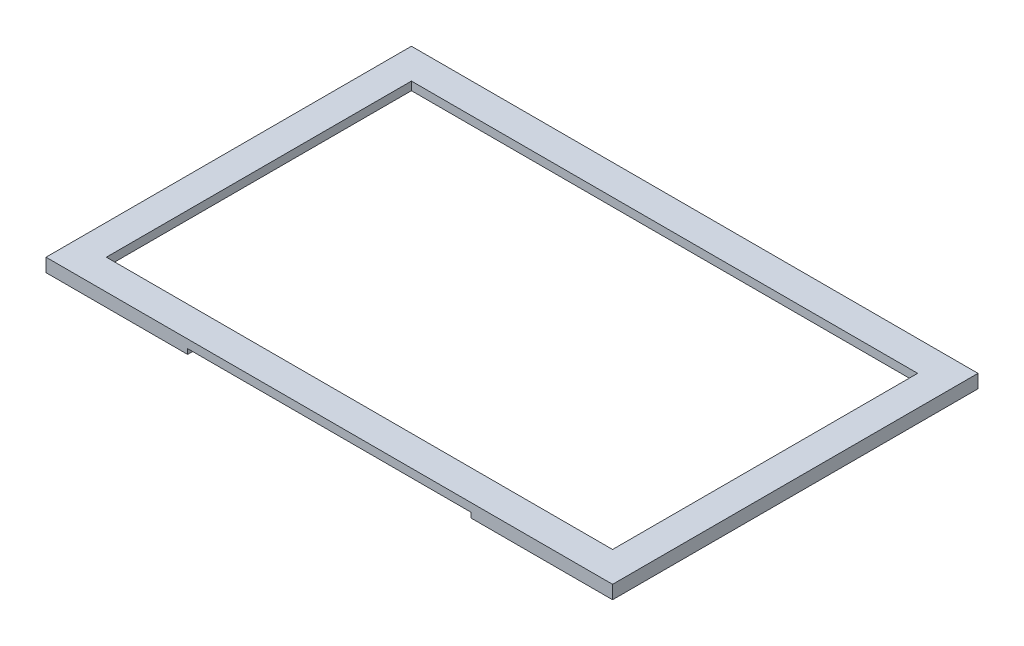
SolidWorks part; units mm, degrees
ref_plane "Front Plane" through (0, 0, 0) normal (0, 0, 1) x (1, 0, 0)
ref_plane "Top Plane" through (0, 0, 0) normal (0, 1, 0) x (1, 0, 0)
ref_plane "Right Plane" through (0, 0, 0) normal (1, 0, 0) x (0, 0, -1)
sketch "Sketch1" plane through (0, 0, 0) normal (0, 0, 1) x (1, 0, 0)
  line L1 (0, 0) -> (169, 0)
  line L2 (0, 0) -> (0, 4)
  line L3 (0, 4) -> (169, 4)
  line L4 (169, 0) -> (169, 4)
  dimension "D1" = 169
  dimension "D2" = 4
extrude "Boss-Extrude1" add sketch "Sketch1" against normal blind 109
sketch "Sketch3" plane through (0, 0, 0) normal (0, -1, 0) x (1, 0, 0)
  line L2 (169, -109) -> (169, 0) construction
  line L3 (167, -107) -> (2, -107)
  line L4 (167, -107) -> (167, -2)
  line L5 (167, -2) -> (2, -2)
  line L6 (2, -107) -> (2, -2)
  line L7 (167, -107) -> (2, -2) construction
  line L8 (167, -2) -> (2, -107) construction
  line L9 (169, -109) -> (0, -109) construction
  point P0 (84.5, -54.5)
  point P5 (84.5, -54.5)
  dimension "D1" = 84.5
  dimension "D2" = 54.5
  dimension "D3" = 105
  dimension "D4" = 165
extrude "Cut-Extrude1" cut sketch "Sketch3" against normal blind 1.5
sketch "Sketch4" plane through (0, 4, 0) normal (0, 1, 0) x (1, 0, 0)
  line L0 (169, 109) -> (169, 0) construction
  line L1 (169, 0) -> (0, 0) construction
  line L3 (160, 9) -> (9, 9)
  line L4 (160, 9) -> (160, 100)
  line L5 (160, 100) -> (9, 100)
  line L6 (9, 9) -> (9, 100)
  line L7 (160, 9) -> (9, 100) construction
  line L8 (160, 100) -> (9, 9) construction
  point P0 (84.5, 54.5)
  point P5 (84.5, 54.5)
  dimension "D1" = 84.5
  dimension "D2" = 54.5
  dimension "D3" = 151
  dimension "D4" = 91
extrude "Cut-Extrude2" cut sketch "Sketch4" against normal blind 5
sketch "Sketch5" plane through (0, 0, 0) normal (0, 0, 1) x (1, 0, 0)
  line L5 (0, 0) -> (169, 0) construction
  line L6 (0, 4) -> (0, 0) construction
  line L8 (42.25, 0) -> (126.75, 0)
  line L9 (42.25, 0) -> (42.25, 1.5)
  line L10 (42.25, 1.5) -> (126.75, 1.5)
  line L11 (126.75, 0) -> (126.75, 1.5)
  point P0 (42.25, 0)
  dimension "D1" = 42.25
  dimension "D2" = 84.5
  dimension "D3" = 1.5
extrude "Cut-Extrude3" cut sketch "Sketch5" against normal blind 2
